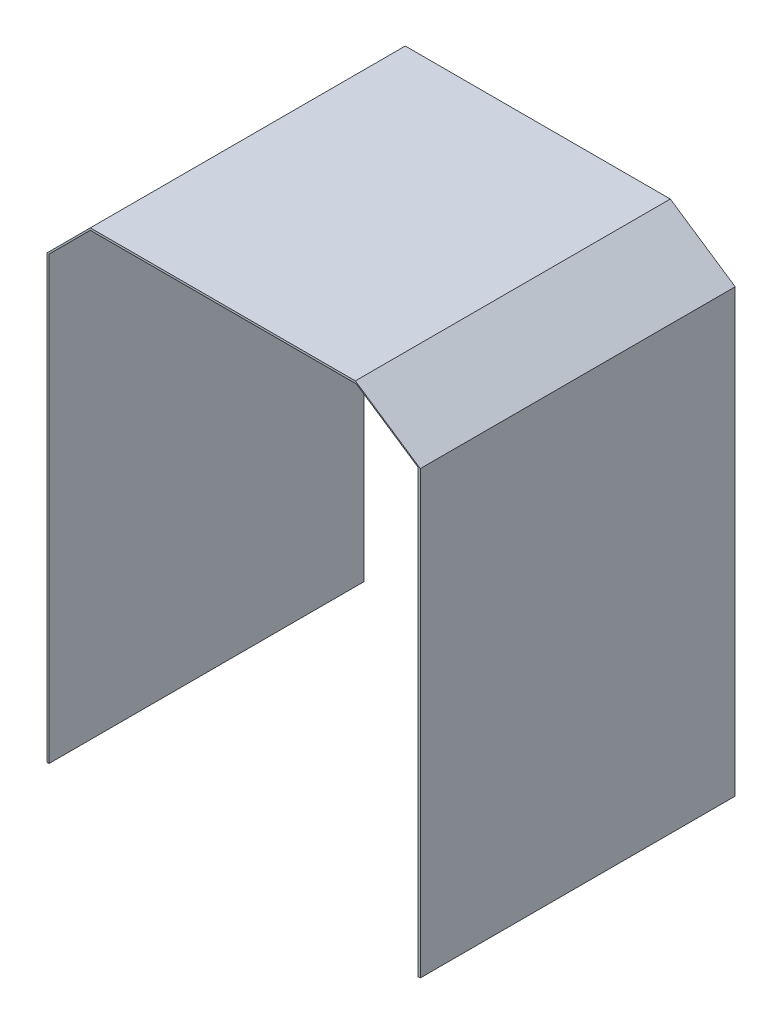
SolidWorks part; units mm, degrees
ref_plane "Front Plane" through (0, 0, 0) normal (0, 0, 1) x (1, 0, 0)
ref_plane "Top Plane" through (0, 0, 0) normal (0, 1, 0) x (1, 0, 0)
ref_plane "Right Plane" through (0, 0, 0) normal (1, 0, 0) x (0, 0, -1)
sketch "Sketch1" plane through (0, 0, 0) normal (0, 0, 1) x (1, 0, 0)
  line L0 (0, 0) -> (0, 45.1)
  line L1 (0, 0) -> (0.22, 0)
  line L2 (0.22, 0) -> (0.22, 45.1)
  line L3 (0.22, 45.1) -> (4.4506, 49.3306)
  line L4 (4.4506, 49.3306) -> (31.6554, 49.3306)
  line L5 (31.6554, 49.3306) -> (37.9636, 45.1)
  line L6 (37.9636, 45.1) -> (37.9636, 0)
  line L7 (37.9636, 0) -> (38.1836, 0)
  line L8 (38.1836, 0) -> (38.1836, 45.1)
  line L9 (38.1836, 45.1) -> (31.5474, 49.5506)
  line L10 (31.5474, 49.5506) -> (4.4506, 49.5506)
  line L11 (4.4506, 49.5506) -> (0, 45.1)
  dimension "D1" = 45.1
  dimension "D2" = 0.22
  dimension "D3" = 0.22
  dimension "D4" = 0.22
  dimension "D5" = 45.1
  dimension "D6" = 45.1
extrude "Boss-Extrude1" add sketch "Sketch1" along normal blind 32.2
